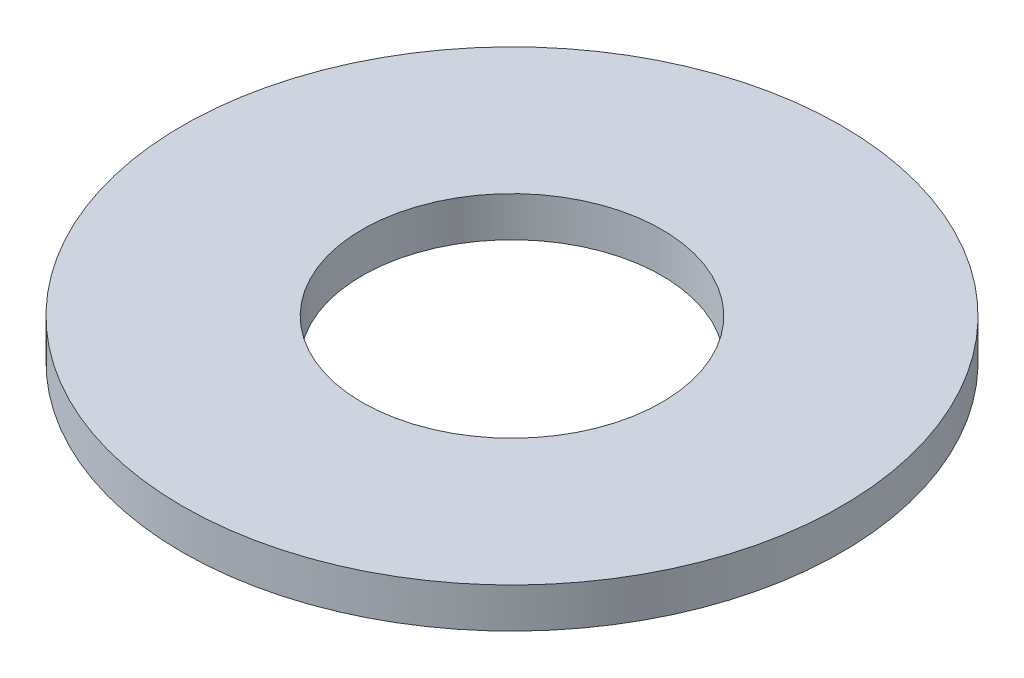
SolidWorks part; units mm, degrees
ref_plane "Front Plane" through (0, 0, 0) normal (0, 0, 1) x (1, 0, 0)
ref_plane "Top Plane" through (0, 0, 0) normal (0, 1, 0) x (1, 0, 0)
ref_plane "Right Plane" through (0, 0, 0) normal (1, 0, 0) x (0, 0, -1)
sketch "Sketch1" plane through (0, 0, 0) normal (0, 1, 0) x (1, 0, 0)
  circle A0 centre (0, 0) radius 37.5
  circle A1 centre (0, 0) radius 82.5
  dimension "D1" = 75
  dimension "D2" = 165
extrude "Boss-Extrude1" add sketch "Sketch1" along normal blind 10
